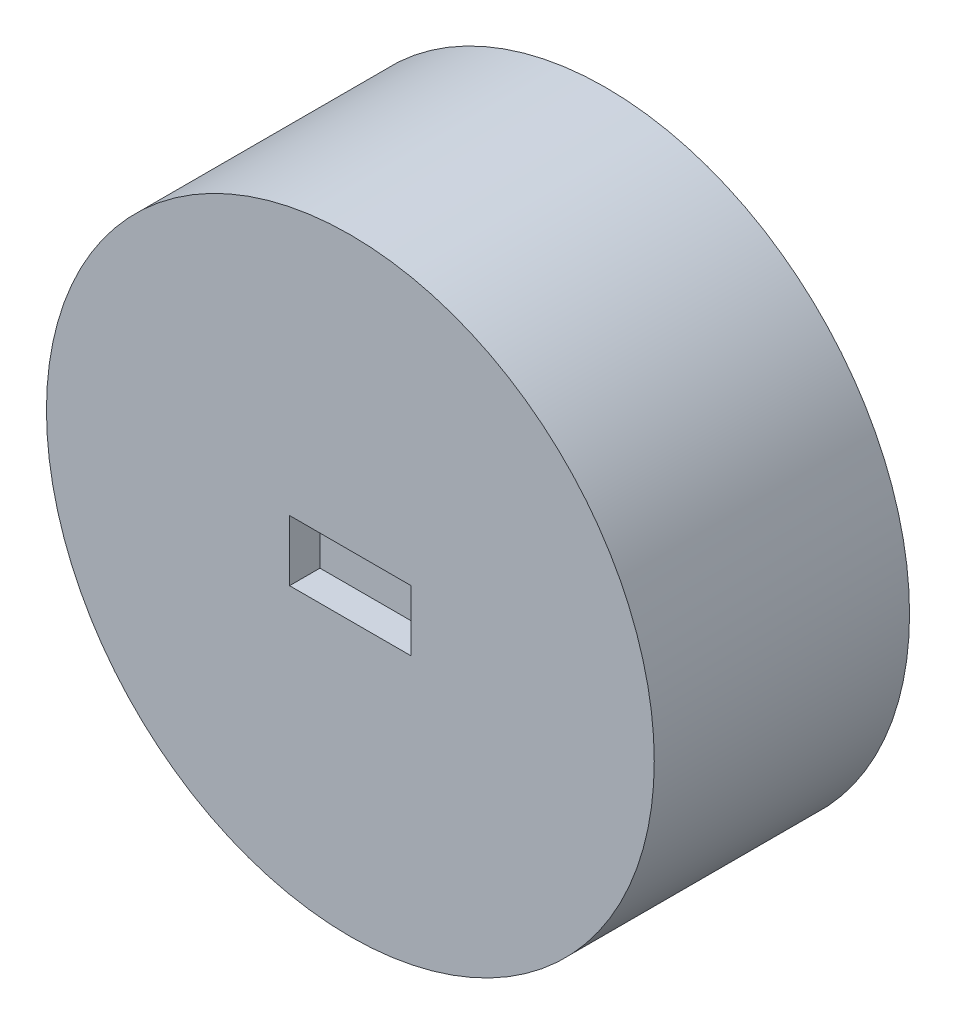
SolidWorks part; units mm, degrees
ref_plane "Front Plane" through (0, 0, 0) normal (0, 0, 1) x (1, 0, 0)
ref_plane "Top Plane" through (0, 0, 0) normal (0, 1, 0) x (1, 0, 0)
ref_plane "Right Plane" through (0, 0, 0) normal (1, 0, 0) x (0, 0, -1)
sketch "Sketch1" plane through (0, 0, 0) normal (0, 0, 1) x (1, 0, 0)
  circle A0 centre (0, 0) radius 50
extrude "Boss-Extrude2" add sketch "Sketch1" along normal blind 42
sketch "Sketch2" plane through (0, 0, 0) normal (0, 0, -1) x (-1, 0, 0)
  circle A0 centre (0, 0) radius 4
extrude "Cut-Extrude1" cut sketch "Sketch2" against normal blind 10
sketch "Sketch3" plane through (0, 0, 42) normal (0, 0, 1) x (1, 0, 0)
  line L1 (-10, -5) -> (10, -5)
  line L2 (-10, -5) -> (-10, 5)
  line L3 (-10, 5) -> (10, 5)
  line L4 (10, -5) -> (10, 5)
  line L5 (-10, -5) -> (10, 5) construction
  line L6 (-10, 5) -> (10, -5) construction
  point P0 (0, 0)
  dimension "D1" = 10
  dimension "D2" = 20
extrude "Cut-Extrude3" cut sketch "Sketch3" against normal blind 5
